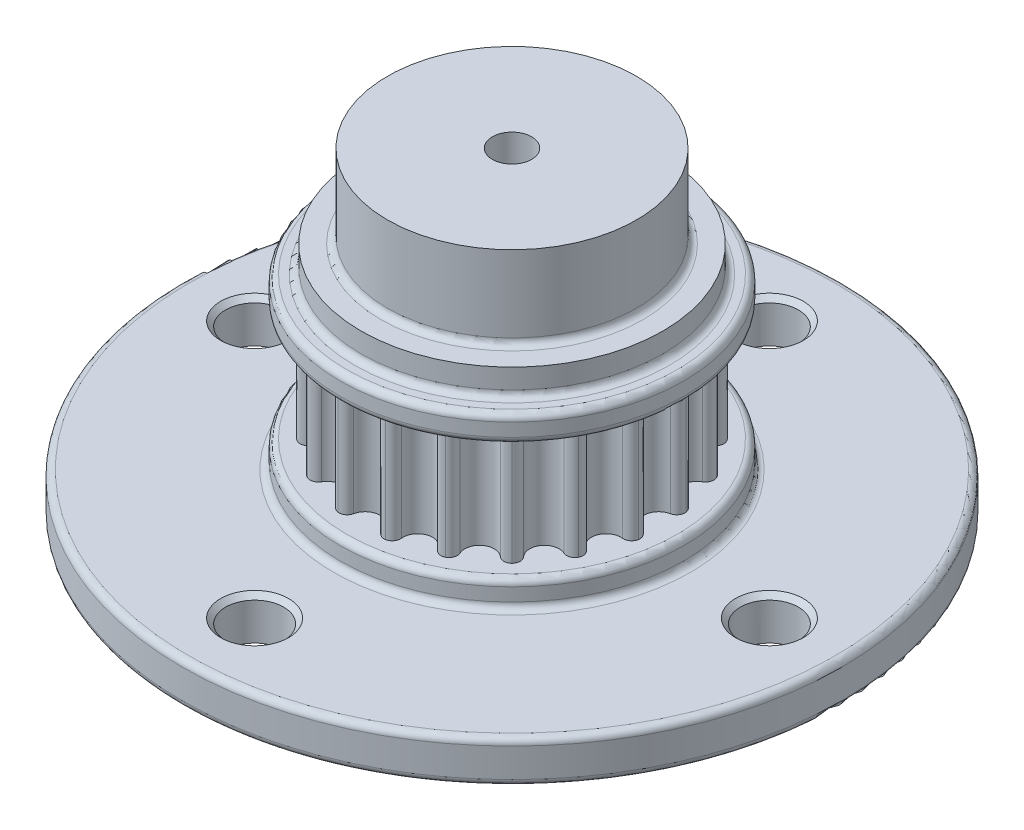
SolidWorks part; units mm, degrees
ref_plane "Front Plane" through (0, 0, 0) normal (0, 0, 1) x (1, 0, 0)
ref_plane "Top Plane" through (0, 0, 0) normal (0, 1, 0) x (1, 0, 0)
ref_plane "Right Plane" through (0, 0, 0) normal (1, 0, 0) x (0, 0, -1)
sketch "Sketch1" plane through (0, 0, 0) normal (0, 1, 0) x (1, 0, 0)
  line L0 (0, 0) -> (0, 9.1676) construction
  line L1 (0, 0) -> (2.731, 8.405) construction
  circle A0 centre (0, 0) radius 9.1676 construction
  circle A1 centre (0, 0) radius 7.9476 construction
  circle A2 centre (0, 8.8376) radius 0.89 construction
  circle A5 centre (2.731, 8.405) radius 0.89 construction
  arc A6 (0, 7.9476) -> (0.8721, 8.6598) centre (0, 8.8376) ccw
  arc A7 (0.8721, 8.6598) -> (1.4405, 9.0537) centre (1.362, 8.5599) cw
  arc A8 (1.4277, 9.0557) -> (1.8466, 8.5054) centre (1.3498, 8.5618) cw
  arc A9 (2.4559, 7.5586) -> (1.8466, 8.5054) centre (2.731, 8.405) cw
  arc A10 (1.4405, 9.0537) -> (1.4277, 9.0557) centre (0, 0) cw
  arc A11 (0, 7.9476) -> (2.4559, 7.5586) centre (0, 0) ccw
  dimension "D1" = 18.3352
  dimension "D3" = 1.78
  dimension "D4" = 0.5
  dimension "D2" = 1.22
  dimension "D5" = 18
extrude "Boss-Extrude1" add sketch "Sketch1" along normal mid plane 7.112 contours A6 A11 A9 A8 A7
ref_axis "Axis1" through (0, 3.3, 0) along (0, -1, 0)
pattern_circular "CirPattern1" count 20 over 360 about axis through (0, 0, 0) along (0, 1, 0) of "Boss-Extrude1"
sketch "Sketch2" plane through (0, 0, 0) normal (1, 0, 0) x (0, 0, -1)
  line L10 (0, 3.5) -> (10.3423, 3.5) construction
  line L11 (0, 3.5) -> (0, 5.0875) construction
  line L12 (0, 5.0875) -> (10.3423, 5.0875)
  line L15 (10.3423, 3.5) -> (10.3423, 5.0875) construction
  line L20 (0, 3.3) -> (0, -3.3) construction
  line L22 (10.3423, 5.0875) -> (0, 5.0875) construction
  line L23 (10.3423, 5.0875) -> (10.3423, 3.5)
  line L24 (10.3423, 3.5) -> (0, 3.5)
  line L25 (0, 5.0875) -> (0, 3.5)
  dimension "D1" = 1.5875
  dimension "D2" = 10.3423
  dimension "D3" = 3.5
revolve "Revolve3" add sketch "Sketch2" angle 360 about axis through (0, 3.3, 0) along (0, -1, 0)
mirror "Mirror1" about plane through (0, 0, 0) normal (0, 1, 0) of "Revolve3"
sketch "Sketch9" plane through (0, -5.0875, 0) normal (0, -1, 0) x (1, 0, 0)
  circle A0 centre (0, 0) radius 19.8438
  circle A1 centre (0, 0) radius 1.5
  dimension "D1" = 3
  dimension "D2" = 39.6875
extrude "Boss-Extrude2" add sketch "Sketch9" along normal blind 2.54
sketch "Sketch3" plane through (0, 0, 0) normal (0, 1, 0) x (1, 0, 0)
  circle A0 centre (-15.5, 0) radius 1.7462
  circle A3 centre (0, 15.5) radius 1.7462
  circle A4 centre (15.5, 0) radius 1.7463
  circle A5 centre (0, -15.5) radius 1.7462
  dimension "D3" = 3.4925
  dimension "D1" = 15.5
  dimension "D4" = 4
extrude "Cut-Extrude1" cut sketch "Sketch3" against normal through all both and the other way through all
ref_axis "Axis2" through (-15.5, -7.6275, 0) along (0, 1, 0)
sketch "Sketch6" plane through (0, 0, 0) normal (0, 0, 1) x (1, 0, 0)
  line L0 (-19.1322, -3.5) -> (-11.8678, -3.5) construction
  line L1 (-5.7956, -3.5) -> (-6.4824, -3.5) construction
  line L2 (-11.8678, -3.5) -> (-15.5, -7.1322)
  line L3 (-15.5, -7.1322) -> (-19.1322, -3.5) construction
  line L4 (-18.548, -4.0842) -> (-12.452, -4.0842) construction
  line L5 (-17.2462, -3.998) -> (-13.7538, -3.998) construction
  line L8 (-15.5, -7.1322) -> (-15.5, -3.5)
  line L9 (-15.5, -3.5) -> (-11.8678, -3.5)
  line L10 (-15.5, -7.6275) -> (-15.5, -5.0875) construction
  line L12 (-17.2462, -5.0875) -> (-17.2462, -7.6275) construction
  line L13 (-13.7538, -7.6275) -> (-13.7538, -5.0875) construction
  point P2 (-15.5, -3.998)
  dimension "D1" = 6.096
  dimension "D2" = 0.5842
revolve "Cut-Revolve2" cut sketch "Sketch6" angle 360 about axis through (-15.5, -7.6275, 0) along (0, 1, 0)
pattern_circular "CirPattern2" count 4 over 360 about axis through (0, 0, 0) along (0, 1, 0) of "Cut-Revolve2"
sketch "Sketch11" plane through (0, -5.0875, 0) normal (0, -1, 0) x (1, 0, 0)
  circle A0 centre (0, 0) radius 1.5
  dimension "D1" = 3
extrude "Cut-Extrude2" cut sketch "Sketch11" against normal blind 6
sketch "Sketch10" plane through (0, 0, 0) normal (1, 0, 0) x (0, 0, -1)
  line L1 (1.1822, 6.675) -> (7.5, 6.675) construction
  line L2 (1.1822, 6.675) -> (1.1822, 11.675)
  line L3 (1.1822, 11.675) -> (7.5, 11.675)
  line L4 (7.5, 6.675) -> (7.5, 11.675)
  line L5 (0, 0) -> (0, 11.675) construction
  line L6 (10.3423, 5.0875) -> (-10.3423, 5.0875) construction
  line L7 (1.1822, 6.675) -> (9.0875, 6.675) construction
  line L8 (1.1822, 6.675) -> (1.1822, 5.0875)
  line L9 (1.1822, 5.0875) -> (9.0875, 5.0875)
  line L10 (9.0875, 6.675) -> (9.0875, 5.0875)
  line L11 (7.5, 6.675) -> (9.0875, 6.675)
  line L12 (0, 11.675) -> (1.1822, 11.675) construction
  dimension "D1" = 2.3644
  dimension "D2" = 5
  dimension "D3" = 1.5875
  dimension "D4" = 1.5875
  dimension "D5" = 15
revolve "Revolve4" add sketch "Sketch10" angle 360 about L5
fillet "Fillet1" radius 0.3969 8 edges at (0, 5.0875, 10.3423) (0, 3.5, 10.3423) (0, -7.6275, -19.8438) (0, -5.0875, -19.8438) (0, 6.675, -7.5) (0, 5.0875, -9.0875) (0, -3.5, 10.3423) (0, -5.0875, 10.3423)
equation "\"TEETH_NUM\"= 20"
equation "\"TOOTH_PITCH\"= 3mm"
equation "\"PITCH_LINE_OFFSET\"= .015in"
equation "\"DIAMETER_PER_GROOVE\"= \"OUTSIDE_DIAMETER\" / \"TEETH_NUM\" * 1in"
equation "\"PITCH_DIAMETER\"= ( ( \"TEETH_NUM\" * 3 - 1.31 ) / 3.1415 + .415 ) * 1mm"
equation "\"OUTSIDE_DIAMETER\"= \"PITCH_DIAMETER\" - \"PITCH_LINE_OFFSET\" * 2"
equation "\"D1@Sketch1\"=\"OUTSIDE_DIAMETER\""
equation "\"TOOTH_HEIGHT\"= 1.22mm"
equation "\"D2@Sketch1\"=\"TOOTH_HEIGHT\""
equation "\"TOOTH_DIAMETER\"= 1.78mm"
equation "\"INTERNAL_RADIUS\"= .5mm"
equation "\"D3@Sketch1\"=\"TOOTH_DIAMETER\""
equation "\"D5@Sketch1\"=360 / \"TEETH_NUM\""
equation "\"D4@Sketch1\"=\"INTERNAL_RADIUS\""
equation "\"D1@CirPattern1\"=\"TEETH_NUM\""
equation "\"BELT_GAP\"= 7mm"
equation "\"D2@Sketch2\"=\"PITCH_DIAMETER\"/2+1/32"
equation "\"D3@Sketch2\"=\"BELT_GAP\"/2"
